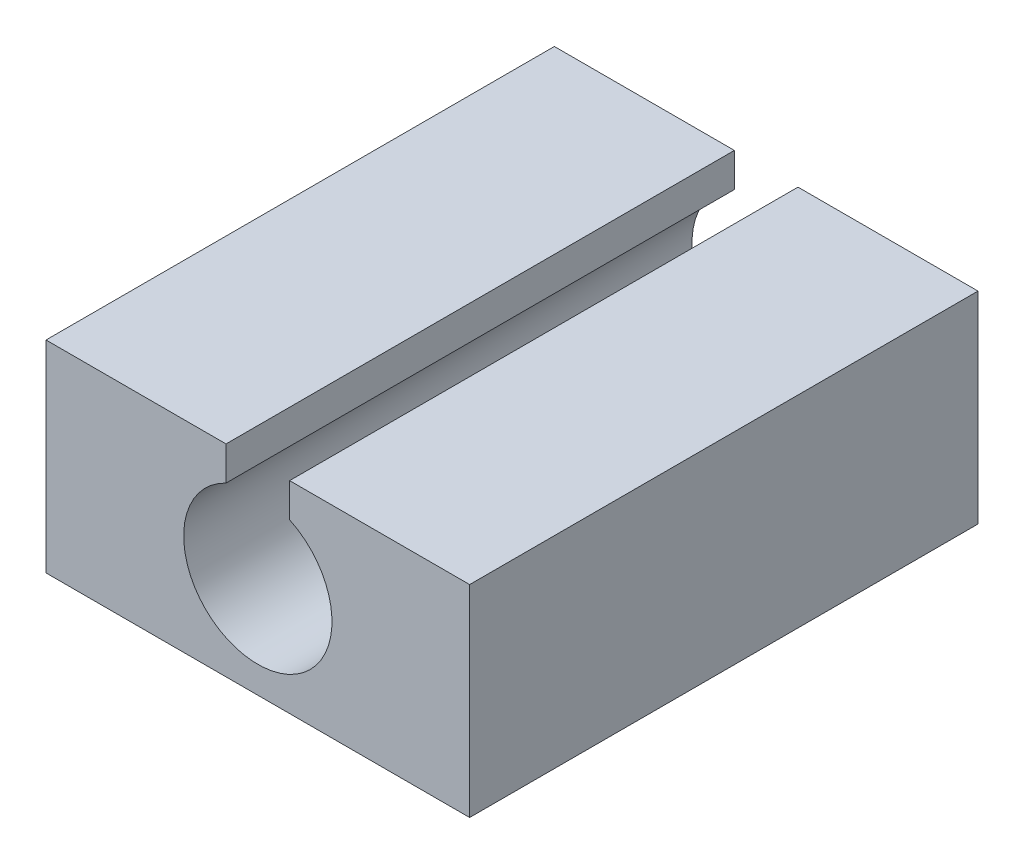
SolidWorks part; units mm, degrees
material "Copper"
ref_plane "Front Plane" through (0, 0, 0) normal (0, 0, 1) x (1, 0, 0)
ref_plane "Top Plane" through (0, 0, 0) normal (0, 1, 0) x (1, 0, 0)
ref_plane "Right Plane" through (0, 0, 0) normal (1, 0, 0) x (0, 0, -1)
sketch "Sketch1" plane through (0, 0, 0) normal (0, 1, 0) x (1, 0, 0)
  line L1 (0, 0) -> (10, 0)
  line L2 (0, 0) -> (0, 12)
  line L3 (0, 12) -> (10, 12)
  line L4 (10, 0) -> (10, 12)
extrude "Boss-Extrude1" add sketch "Sketch1" along normal blind 4.7625
sketch "Sketch2" plane through (0, 0, 0) normal (0, 0, 1) x (1, 0, 0)
  line L0 (0, 2.3813) -> (10, 2.3813) construction
  line L1 (0, 4.7625) -> (0, 0) construction
  line L2 (10, 4.7625) -> (10, 0) construction
  line L3 (5, 4.7625) -> (5, 0) construction
  line L4 (0, 4.7625) -> (10, 4.7625) construction
  circle A0 centre (5, 2.3813) radius 1.75
extrude "Cut-Extrude1" cut sketch "Sketch2" against normal blind 12.7625
sketch "Sketch4" plane through (0, 4.7625, 0) normal (0, 1, 0) x (1, 0, 0)
  line L0 (5, 12) -> (5, 0) construction
  line L1 (10, 12) -> (0, 12) construction
  line L2 (0, 0) -> (10, 0) construction
  line L3 (0, 6) -> (10, 6) construction
  line L4 (0, 12) -> (0, 0) construction
  line L5 (10, 0) -> (10, 12) construction
  line L7 (4.2494, 12) -> (5.7506, 12)
  line L8 (4.2494, 12) -> (4.2494, 0)
  line L9 (4.2494, 0) -> (5.7506, 0)
  line L10 (5.7506, 12) -> (5.7506, 0)
  line L11 (4.2494, 12) -> (5.7506, 0) construction
  line L12 (4.2494, 0) -> (5.7506, 12) construction
  point P12 (5, 6)
extrude "Cut-Extrude2" cut sketch "Sketch4" against normal blind 1
sketch "Sketch5" plane through (0, 0, 0) normal (0, 0, 1) x (1, 0, 0)
  line L0 (0.3812, 4.7625) -> (0.3812, 0) construction
  line L1 (0, 4.3623) -> (10, 4.3623) construction
  line L2 (0, 4.7625) -> (5, 0) construction
  line L3 (0, 0) -> (10, 0) construction
  line L4 (5, 0) -> (10, 4.7625) construction
  line L5 (5.7506, 4.7625) -> (10, 4.7625) construction
  line L6 (10, 4.7625) -> (10, 0) construction
  line L7 (0, 4.7625) -> (0, 4.3623) construction
  line L8 (0, 4.7625) -> (0, 0) construction
  line L9 (0, 4.3623) -> (0.3812, 4.7625) construction
  line L10 (0, 4.7625) -> (4.2494, 4.7625) construction
  line L11 (10, 4.7625) -> (10, 4.3623) construction
  line L12 (10, 4.3623) -> (9.5799, 4.7625) construction
  line L13 (9.5799, 4.7625) -> (9.5799, 0) construction
  line L14 (10, 0) -> (10, 0.4) construction
  line L15 (10, 0.4) -> (0, 0.4) construction
  line L16 (0, 4.3623) -> (0, 4.7625) construction
  line L17 (0, 4.7625) -> (0.3812, 4.7625) construction
  line L18 (10, 4.3623) -> (10, 4.7625) construction
  line L19 (10, 4.7625) -> (9.5799, 4.7625) construction
  line L20 (9.5799, 0) -> (10, 0) construction
  line L21 (10, 0) -> (10, 0.4) construction
  line L22 (0.3812, 0) -> (0, 0) construction
  line L23 (0, 0) -> (0, 0.4) construction
  line L24 (4.2494, 3.9621) -> (3.6497, 4.7625) construction
  line L25 (5.7506, 3.9621) -> (6.3431, 4.7625) construction
  line L26 (4.2494, 3.9621) -> (4.2494, 4.7625) construction
  line L28 (4.2494, 4.7625) -> (3.6497, 4.7625) construction
  line L29 (5.7506, 3.9621) -> (5.7506, 4.7625) construction
  line L31 (5.7506, 4.7625) -> (6.3431, 4.7625) construction
  spline S0 degree 2 poles (0, 4.3623) (0, 4.7625) (0.3812, 4.7625) knots 0 0 0 1 1 1
  spline S1 degree 2 poles (10, 4.3623) (10, 4.7625) (9.5799, 4.7625) knots 0 0 0 1 1 1
  spline S2 degree 2 poles (9.5799, 0) (10, 0) (10, 0.4) knots 0 0 0 1 1 1
  spline S3 degree 2 poles (0.3812, 0) (0, 0) (0, 0.4) knots 0 0 0 1 1 1
  spline S4 degree 2 poles (4.2494, 3.9621) (4.2494, 4.7625) (3.6497, 4.7625) knots 0 0 0 1 1 1
  spline S5 degree 2 poles (5.7506, 3.9621) (5.7506, 4.7625) (6.3431, 4.7625) knots 0 0 0 1 1 1
